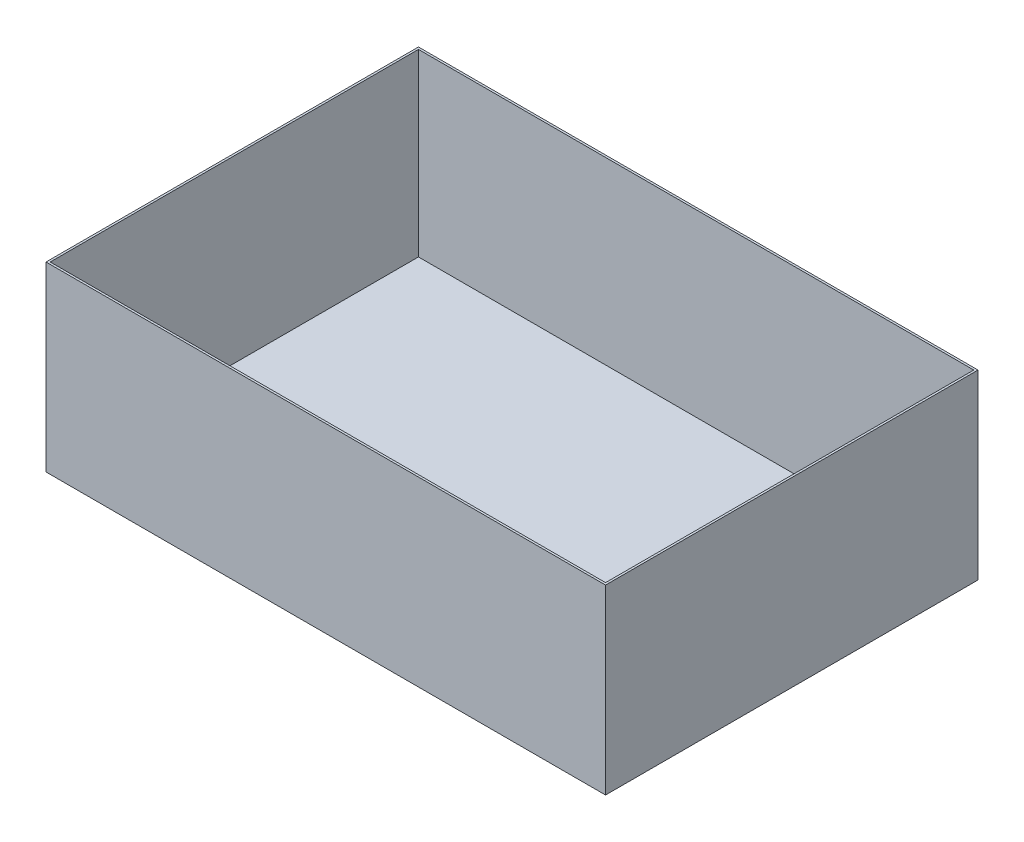
SolidWorks part; units mm, degrees
ref_plane "Front Plane" through (0, 0, 0) normal (0, 0, 1) x (1, 0, 0)
ref_plane "Top Plane" through (0, 0, 0) normal (0, 1, 0) x (1, 0, 0)
ref_plane "Right Plane" through (0, 0, 0) normal (1, 0, 0) x (0, 0, -1)
sketch "Sketch2" plane through (0, 0, 0) normal (0, 1, 0) x (1, 0, 0)
  line L1 (0, 0) -> (600, 0)
  line L2 (0, 0) -> (0, 399.38)
  line L3 (0, 399.38) -> (600, 399.38)
  line L4 (600, 0) -> (600, 399.38)
  dimension "D1" = 600
  dimension "D2" = 399.38
extrude "Boss-Extrude1" add sketch "Sketch2" along normal blind 195
shell "Shell1" thickness 2.25
